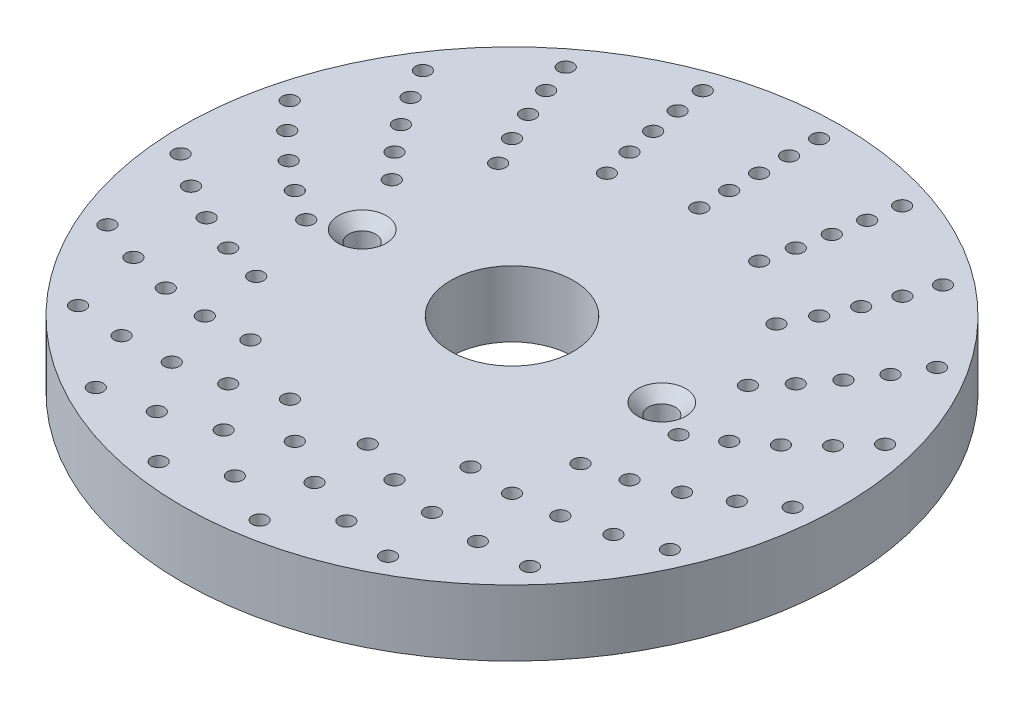
SolidWorks part; units mm, degrees
ref_plane "Alzado" through (0, 0, 0) normal (0, 0, 1) x (1, 0, 0)
ref_plane "Planta" through (0, 0, 0) normal (0, 1, 0) x (1, 0, 0)
ref_plane "Vista lateral" through (0, 0, 0) normal (1, 0, 0) x (0, 0, -1)
sketch "Croquis1" plane through (0, 0, 0) normal (0, 1, 0) x (1, 0, 0)
  circle A0 centre (0, 0) radius 55
  dimension "D1" = 110
extrude "Saliente-Extruir1" add sketch "Croquis1" along normal mid plane 11
sketch "Croquis2" plane through (0, 0, 0) normal (0, 0, 1) x (1, 0, 0)
  line L0 (0, 27.4757) -> (0, -22.0914) construction
  line L1 (-25, 24.9419) -> (-25, -22.0914) construction
  line L2 (-25, 5.5) -> (-29, 5.5)
  line L3 (55, 5.5) -> (-55, 5.5) construction
  line L4 (-29, 5.5) -> (-27.25, 3.7)
  line L5 (-27.25, 3.7) -> (-27.25, -3.7)
  line L6 (-27.25, -3.7) -> (-29, -5.5)
  line L7 (-29, -5.5) -> (-25, -5.5)
  line L8 (-25, -5.5) -> (-25, 5.5)
  line L9 (-55, -5.5) -> (55, -5.5) construction
  dimension "D1" = 25
  dimension "D2" = 4.5
  dimension "D3" = 8
  dimension "D4" = 8
  dimension "D5" = 1.8
  dimension "D6" = 1.8
revolve "Cortar-Revolución1" cut sketch "Croquis2" angle 360 about L1
mirror "Simetría1" about plane through (0, 0, 0) normal (1, 0, 0) of "Cortar-Revolución1"
sketch "Croquis3" plane through (0, 5.5, 0) normal (0, 1, 0) x (1, 0, 0)
  line L0 (0, 0) -> (0, 31.25) construction
  circle A0 centre (0, 31.25) radius 1.25
  dimension "D2" = 2.5
  dimension "D1" = 31.25
extrude "Cortar-Extruir1" cut sketch "Croquis3" against normal blind 3.5
pattern_circular "MatrizC1" count 15 over 360 about axis through (0, 0, 0) along (0, 1, 0) of "Cortar-Extruir1"
sketch "Croquis4" plane through (0, 5.5, 0) normal (0, 1, 0) x (1, 0, 0)
  line L0 (0, 0) -> (0, 36.25) construction
  circle A0 centre (0, 36.25) radius 1.25
  dimension "D2" = 2.5
  dimension "D1" = 36.25
extrude "Cortar-Extruir2" cut sketch "Croquis4" against normal blind 3.5
pattern_circular "MatrizC2" count 16 over 360 about axis through (0, 0, 0) along (0, 1, 0) of "Cortar-Extruir2"
sketch "Croquis5" plane through (0, 0, 0) normal (0, 1, 0) x (1, 0, 0)
  line L0 (0, 0) -> (0, 41.25) construction
  circle A0 centre (0, 41.25) radius 1.25
  dimension "D2" = 2.5
  dimension "D1" = 41.25
sketch "Croquis6" plane through (0, 5.5, 0) normal (0, 1, 0) x (1, 0, 0)
  circle A0 centre (0, 41.25) radius 1.25 construction
  circle A1 centre (0, 41.25) radius 1.25
extrude "Cortar-Extruir4" cut sketch "Croquis6" against normal blind 3.5
pattern_circular "MatrizC3" count 17 over 360 about axis through (0, 0, 0) along (0, 1, 0) of "Cortar-Extruir4"
sketch "Croquis7" plane through (0, 5.5, 0) normal (0, 1, 0) x (1, 0, 0)
  line L0 (0, 0) -> (0, 46.25) construction
  circle A0 centre (0, 46.25) radius 1.25
  dimension "D1" = 2.5
  dimension "D2" = 46.25
extrude "Cortar-Extruir5" cut sketch "Croquis7" against normal blind 3.5
pattern_circular "MatrizC4" count 18 over 360 about axis through (0, 0, 0) along (0, 1, 0) of "Cortar-Extruir5"
sketch "Croquis8" plane through (0, 5.5, 0) normal (0, 1, 0) x (1, 0, 0)
  line L0 (0, 0) -> (0, 51.25) construction
  circle A0 centre (0, 51.25) radius 1.25
  dimension "D2" = 2.5
  dimension "D1" = 51.25
extrude "Cortar-Extruir6" cut sketch "Croquis8" against normal blind 3.5
pattern_circular "MatrizC5" count 19 over 360 about axis through (0, 0, 0) along (0, 1, 0) of "Cortar-Extruir6"
sketch "Croquis9" plane through (0, 5.5, 0) normal (0, 1, 0) x (1, 0, 0)
  circle A0 centre (0, 0) radius 10.25
  dimension "D1" = 20.5
extrude "Cortar-Extruir7" cut sketch "Croquis9" against normal blind 36.3
sketch "Croquis10" plane through (0, -5.5, 0) normal (0, -1, 0) x (1, 0, 0)
  line L0 (0, 0) -> (0, -31.25) construction
  circle A0 centre (0, -31.25) radius 1.25
  dimension "D1" = 2.5
extrude "Cortar-Extruir8" cut sketch "Croquis10" against normal blind 3.5
pattern_circular "MatrizC6" count 20 over 360 about axis through (0, 0, 0) along (0, 1, 0) of "Cortar-Extruir8"
sketch "Croquis11" plane through (0, -5.5, 0) normal (0, -1, 0) x (1, 0, 0)
  line L0 (0, 0) -> (0, -36.25) construction
  circle A0 centre (0, -36.25) radius 1.25
  dimension "D1" = 2.5
extrude "Cortar-Extruir9" cut sketch "Croquis11" against normal blind 3.5
pattern_circular "MatrizC7" count 21 over 360 about axis through (0, 0, 0) along (0, 1, 0) of "Cortar-Extruir9"
sketch "Croquis12" plane through (0, -5.5, 0) normal (0, -1, 0) x (1, 0, 0)
  line L0 (0, 0) -> (0, -41.25) construction
  circle A0 centre (0, -41.25) radius 1.25
  dimension "D1" = 2.5
extrude "Cortar-Extruir10" cut sketch "Croquis12" against normal blind 3.5
pattern_circular "MatrizC8" count 23 over 360 about axis through (0, 0, 0) along (0, 1, 0) of "Cortar-Extruir10"
sketch "Croquis13" plane through (0, -5.5, 0) normal (0, -1, 0) x (1, 0, 0)
  line L0 (0, 0) -> (0, -46.25) construction
  circle A0 centre (0, -46.25) radius 1.25
  dimension "D1" = 2.5
extrude "Cortar-Extruir11" cut sketch "Croquis13" against normal blind 3.5
pattern_circular "MatrizC9" count 27 over 360 about axis through (0, 0, 0) along (0, 1, 0) of "Cortar-Extruir11"
sketch "Croquis14" plane through (0, -5.5, 0) normal (0, -1, 0) x (1, 0, 0)
  line L0 (0, 0) -> (0, -51.25) construction
  circle A0 centre (0, -51.25) radius 1.25
  dimension "D1" = 2.5
extrude "Cortar-Extruir12" cut sketch "Croquis14" against normal blind 3.5
pattern_circular "MatrizC10" count 29 over 360 about axis through (0, 0, 0) along (0, 1, 0) of "Cortar-Extruir12"
